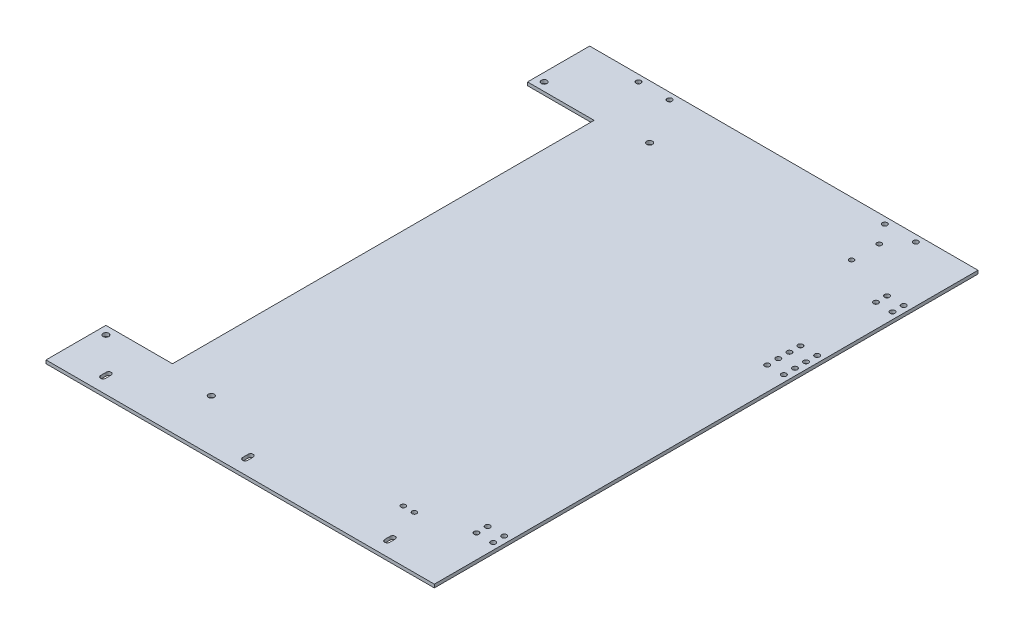
SolidWorks part; units mm, degrees
material "6061 合金"
ref_plane "前视基准面" through (0, 0, 0) normal (0, 0, 1) x (1, 0, 0)
ref_plane "上视基准面" through (0, 0, 0) normal (0, 1, 0) x (1, 0, 0)
ref_plane "右视基准面" through (0, 0, 0) normal (1, 0, 0) x (0, 0, -1)
sketch "草图1" plane through (0, 0, 0) normal (0, 0, 1) x (1, 0, 0)
  line L1 (-18.5263, 6.2355) -> (331.4737, 6.2355)
  line L2 (-18.5263, 6.2355) -> (-18.5263, 3.2355)
  line L3 (-18.5263, 3.2355) -> (331.4737, 3.2355)
  line L4 (331.4737, 6.2355) -> (331.4737, 3.2355)
  dimension "D1" = 3
  dimension "D2" = 350
extrude "凸台-拉伸1" add sketch "草图1" along normal blind 490
sketch "草图2" plane through (0, 6.2355, 0) normal (0, 1, 0) x (1, 0, 0)
  line L0 (331.4737, -490) -> (-18.5263, -490) construction
  line L1 (411.2526, -48.5) -> (-140.5458, -48.5) construction
  line L2 (411.2526, -443.5) -> (-140.5458, -443.5) construction
  line L3 (331.4737, 0) -> (-18.5263, 0) construction
  line L4 (282.235, -426) -> (377.0462, -426) construction
  line L5 (-18.5263, -490) -> (-18.5263, 0) construction
  line L6 (290.5463, -164) -> (372.497, -164) construction
  line L7 (-18.5263, -56) -> (41.4737, -56)
  line L8 (-18.5263, -56) -> (-18.5263, -436)
  line L9 (-18.5263, -436) -> (41.4737, -436)
  line L10 (41.4737, -56) -> (41.4737, -436)
  line L11 (372.497, -144) -> (290.5463, -144) construction
  line L12 (331.4737, -490) -> (331.4737, 0) construction
  line L13 (331.4737, -490) -> (331.4737, 0) construction
  line L14 (367.4379, -66) -> (282.235, -66) construction
  line L15 (377.0462, -105) -> (282.235, -105) construction
  line L16 (344.9341, -6) -> (-30.3419, -6) construction
  line L17 (156.4737, -114.4028) -> (156.4737, 89.021) construction
  line L18 (398.0842, -475) -> (-112.6474, -475) construction
  line L19 (276.4737, -458.0065) -> (276.4737, -487.6575) construction
  line L21 (274.2237, -472.5) -> (274.2237, -477.5)
  line L23 (278.7237, -472.5) -> (278.7237, -477.5)
  line L24 (146.2237, -472.5) -> (146.2237, -477.5)
  line L25 (148.4737, -458.0065) -> (148.4737, -487.6575) construction
  line L26 (150.7237, -472.5) -> (150.7237, -477.5)
  line L27 (18.2237, -472.5) -> (18.2237, -477.5)
  line L28 (20.4737, -458.0065) -> (20.4737, -487.6575) construction
  line L29 (22.7237, -472.5) -> (22.7237, -477.5)
  line L30 (398.0842, -246) -> (246.0095, -246) construction
  line L31 (266.4737, -20.9233) -> (266.4737, -458.0065) construction
  circle A0 centre (-11.0263, -48.5) radius 2.6
  circle A1 centre (83.9737, -48.5) radius 2.6
  circle A2 centre (-11.0263, -443.5) radius 2.6
  circle A3 centre (83.9737, -443.5) radius 2.6
  circle A4 centre (310.4737, -159) radius 2.25
  circle A5 centre (325.4737, -159) radius 2.25
  circle A6 centre (325.4737, -169) radius 2.25
  circle A7 centre (310.4737, -169) radius 2.25
  circle A8 centre (310.4737, -431) radius 2.25
  circle A9 centre (325.4737, -431) radius 2.25
  circle A10 centre (325.4737, -421) radius 2.25
  circle A11 centre (310.4737, -421) radius 2.25
  circle A13 centre (325.4737, -149) radius 2.25
  circle A14 centre (310.4737, -149) radius 2.25
  circle A15 centre (310.4737, -139) radius 2.25
  circle A16 centre (325.4737, -139) radius 2.25
  circle A17 centre (310.4737, -71) radius 2.25
  circle A18 centre (310.4737, -61) radius 2.25
  circle A19 centre (325.4737, -61) radius 2.25
  circle A20 centre (325.4737, -71) radius 2.25
  circle A21 centre (281.4737, -6) radius 2.25
  circle A22 centre (253.4737, -6) radius 2.25
  circle A23 centre (31.4737, -6) radius 2.25
  circle A24 centre (59.4737, -6) radius 2.25
  arc A25 (278.7237, -472.5) -> (274.2237, -472.5) centre (276.4737, -472.5) ccw
  arc A26 (274.2237, -477.5) -> (278.7237, -477.5) centre (276.4737, -477.5) ccw
  arc A27 (150.7237, -472.5) -> (146.2237, -472.5) centre (148.4737, -472.5) ccw
  arc A28 (146.2237, -477.5) -> (150.7237, -477.5) centre (148.4737, -477.5) ccw
  arc A29 (22.7237, -472.5) -> (18.2237, -472.5) centre (20.4737, -472.5) ccw
  arc A30 (18.2237, -477.5) -> (22.7237, -477.5) centre (20.4737, -477.5) ccw
  circle A31 centre (266.4737, -24) radius 2.1
  circle A32 centre (266.4737, -49) radius 2.1
  circle A33 centre (266.4737, -443) radius 2.1
  circle A35 centre (256.4737, -443) radius 2.1
  dimension "D3" = 5.2
  dimension "D4" = 95
  dimension "D5" = 7.5
  dimension "D6" = 95
  dimension "D7" = 7.5
  dimension "D8" = 5.2
  dimension "D14" = 15
  dimension "D15" = 6
  dimension "D16" = 4.5
  dimension "D17" = 5
  dimension "D18" = 2
  dimension "D21" = 5
  dimension "D22" = 4.5
  dimension "D26" = 28
  dimension "D27" = 50
  dimension "D28" = 4.5
  dimension "D30" = 4.5
  dimension "D33" = 4.5
  dimension "D36" = 4.5
  dimension "D42" = 4.2
  dimension "D43" = 25
  dimension "D44" = 394
  dimension "D46" = 10
  dimension "D1" = 48.5
  dimension "D2" = 46.5
  dimension "D9" = 7.5
  dimension "D10" = 7.5
  dimension "D11" = 60
  dimension "D12" = 262
  dimension "D13" = 17.5
  dimension "D19" = 15
  dimension "D20" = 6
  dimension "D23" = 20
  dimension "D24" = 17.5
  dimension "D25" = 6
  dimension "D29" = 15
  dimension "D31" = 5
  dimension "D32" = 4.5
  dimension "D34" = 5
  dimension "D35" = 4.5
  dimension "D37" = 5
  dimension "D38" = 4.5
  dimension "D39" = 55
  dimension "D40" = 128
  dimension "D41" = 128
  dimension "D45" = 65
extrude "切除-拉伸1" cut sketch "草图2" against normal blind 50
